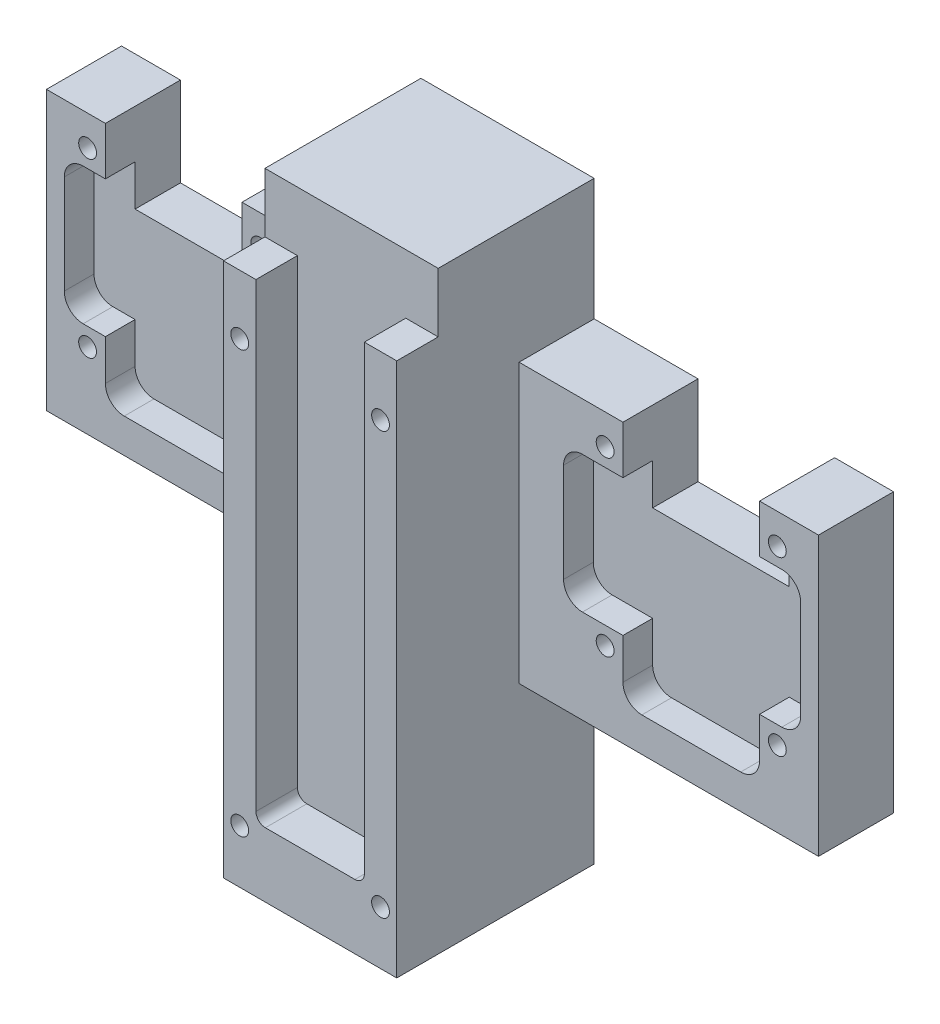
SolidWorks part; units mm, degrees
ref_plane "Front Plane" through (0, 0, 0) normal (0, 0, 1) x (1, 0, 0)
ref_plane "Top Plane" through (0, 0, 0) normal (0, 1, 0) x (1, 0, 0)
ref_plane "Right Plane" through (0, 0, 0) normal (1, 0, 0) x (0, 0, -1)
sketch "Sketch1" plane through (0, 0, 0) normal (0, 0, 1) x (1, 0, 0)
  line L0 (0, 0) -> (130, 0)
  line L1 (0, 0) -> (0, -104.86)
  line L2 (0, -104.86) -> (130, -104.86)
  line L3 (130, -104.86) -> (130, 0)
  dimension "D1" = 130
  dimension "D2" = 104.86
extrude "Boss-Extrude1" add sketch "Sketch1" along normal blind 39.84
sketch "Sketch2" plane through (0, 0, 39.84) normal (0, 0, 1) x (1, 0, 0)
  line L0 (130, 0) -> (130, -94.86)
  line L1 (130, -104.86) -> (130, 0) construction
  line L2 (130, -94.86) -> (0, -94.86)
  line L3 (0, 0) -> (0, -104.86) construction
  line L4 (0, -94.86) -> (0, 0)
  line L5 (0, 0) -> (130, 0)
  dimension "D1" = 94.86
extrude "Cut-Extrude1" cut sketch "Sketch2" against normal blind 6.6
sketch "Sketch3" plane through (0, 0, 33.24) normal (0, 0, 1) x (1, 0, 0)
  line L0 (55.875, 0) -> (55.875, -89.15)
  line L1 (130, 0) -> (0, 0) construction
  line L2 (55.875, -89.15) -> (74.125, -89.15)
  line L3 (74.125, -89.15) -> (74.125, 0)
  line L4 (74.125, 0) -> (55.875, 0)
  line L5 (130, -94.86) -> (130, 0) construction
  dimension "D1" = 18.25
  dimension "D2" = 55.875
  dimension "D3" = 89.15
extrude "Cut-Extrude2" cut sketch "Sketch3" against normal blind 6.98
sketch "Sketch5" plane through (0, 0, 33.24) normal (0, 0, 1) x (1, 0, 0)
  line L0 (79.585, 0) -> (79.585, -94.86)
  line L1 (130, 0) -> (74.125, 0) construction
  line L2 (0, -94.86) -> (130, -94.86) construction
  line L3 (79.585, -94.86) -> (130, -94.86)
  line L4 (130, -94.86) -> (130, 0)
  line L5 (130, 0) -> (79.585, 0)
  line L6 (50.415, 0) -> (50.415, -94.86)
  line L7 (55.875, 0) -> (0, 0) construction
  line L8 (50.415, -94.86) -> (0, -94.86)
  line L9 (0, -94.86) -> (0, 0)
  line L10 (0, 0) -> (50.415, 0)
  line L11 (55.875, 0) -> (55.875, -89.15) construction
  line L12 (74.125, -89.15) -> (74.125, 0) construction
  dimension "D1" = 5.46
  dimension "D2" = 5.46
extrude "Cut-Extrude3" cut sketch "Sketch5" against normal blind 20.6
sketch "Sketch6" plane through (0, 0, 12.64) normal (0, 0, 1) x (1, 0, 0)
  line L0 (50.415, -94.86) -> (50.415, 0) construction
  line L1 (74.125, 0) -> (55.875, 0) construction
  line L2 (79.585, 0) -> (79.585, -94.86) construction
  circle A0 centre (35.925, -25.6) radius 1.5
  circle A1 centre (6.925, -25.6) radius 1.5
  circle A2 centre (35.925, -54.6) radius 1.5
  circle A3 centre (6.925, -54.6) radius 1.5
  circle A4 centre (94.075, -25.6) radius 1.5
  circle A5 centre (123.075, -25.6) radius 1.5
  circle A6 centre (94.075, -54.6) radius 1.5
  circle A7 centre (123.075, -54.6) radius 1.5
  dimension "D2" = 3
  dimension "D3" = 25.6
  dimension "D4" = 29
  dimension "D5" = 29
  dimension "D6" = 29
  dimension "D8" = 14.49
  dimension "D9" = 29
  dimension "D10" = 29
  dimension "D11" = 29
  dimension "D1" = 14.49
  dimension "D7" = 29
  dimension "D12" = 29
  dimension "D13" = 25.6
extrude "Cut-Extrude4" cut sketch "Sketch6" against normal blind 12.4
sketch "Sketch7" plane through (0, 0, 12.64) normal (0, 0, 1) x (1, 0, 0)
  line L0 (50.415, -94.86) -> (50.415, 0) construction
  line L1 (0, 0) -> (50.415, 0)
  line L2 (0, 0) -> (0, -20.5)
  line L3 (0, -20.5) -> (50.415, -20.5)
  line L4 (50.415, 0) -> (50.415, -20.5)
  line L5 (130, -94.86) -> (130, 0) construction
  line L6 (79.585, 0) -> (130, 0)
  line L7 (79.585, 0) -> (79.585, -20.5)
  line L8 (79.585, -20.5) -> (130, -20.5)
  line L9 (130, 0) -> (130, -20.5)
  dimension "D1" = 20.5
  dimension "D2" = 20.5
extrude "Cut-Extrude5" cut sketch "Sketch7" against normal blind 12.4
sketch "Sketch9" plane through (0, 0, 12.64) normal (0, 0, 1) x (1, 0, 0)
  line L0 (97.075, -20.5) -> (97.075, -35.5)
  line L1 (79.585, -20.5) -> (130, -20.5) construction
  line L2 (97.075, -35.5) -> (120.075, -35.5)
  line L3 (120.075, -35.5) -> (120.075, -20.5)
  line L4 (120.075, -20.5) -> (97.075, -20.5)
  line L5 (9.925, -20.5) -> (9.925, -35.5)
  line L6 (0, -20.5) -> (50.415, -20.5) construction
  line L7 (9.925, -35.5) -> (32.925, -35.5)
  line L8 (32.925, -35.5) -> (32.925, -20.5)
  line L9 (0, -20.5) -> (50.415, -20.5) construction
  line L10 (32.925, -20.5) -> (9.925, -20.5)
  circle A0 centre (123.075, -25.6) radius 1.5 construction
  circle A1 centre (94.075, -25.6) radius 1.5 construction
  circle A2 centre (6.925, -25.6) radius 1.5 construction
  circle A3 centre (35.925, -25.6) radius 1.5 construction
  dimension "D1" = 3
  dimension "D4" = 3
  dimension "D2" = 3
  dimension "D3" = 15
  dimension "D5" = 3
  dimension "D6" = 15
extrude "Cut-Extrude7" cut sketch "Sketch9" against normal up to surface (12.4 mm away) up to face at (104.7925, -10.25, 0.24)
sketch "Sketch10" plane through (0, 0, 12.64) normal (0, 0, 1) x (1, 0, 0)
  line L0 (9.925, -28.6) -> (3, -28.6)
  line L1 (9.925, -35.5) -> (9.925, -20.5) construction
  line L2 (3, -28.6) -> (3, -51.6)
  line L3 (3, -51.6) -> (9.925, -51.6)
  line L4 (9.925, -51.6) -> (9.925, -61.6)
  line L5 (9.925, -61.6) -> (32.925, -61.6)
  line L6 (32.925, -61.6) -> (32.925, -51.6)
  line L7 (32.925, -51.6) -> (42.925, -51.6)
  line L8 (42.925, -51.6) -> (42.925, -28.6)
  line L9 (42.925, -28.6) -> (32.925, -28.6)
  line L10 (32.925, -35.5) -> (32.925, -20.5) construction
  line L11 (32.925, -28.6) -> (32.925, -35.5)
  line L12 (32.925, -35.5) -> (9.925, -35.5)
  line L13 (32.925, -35.5) -> (9.925, -35.5) construction
  line L14 (9.925, -35.5) -> (9.925, -28.6)
  line L16 (0, -20.5) -> (0, -94.86) construction
  line L17 (97.075, -28.6) -> (87.075, -28.6)
  line L18 (97.075, -20.5) -> (97.075, -35.5) construction
  line L19 (87.075, -28.6) -> (87.075, -51.6)
  line L20 (87.075, -51.6) -> (97.075, -51.6)
  line L21 (97.075, -51.6) -> (97.075, -61.6)
  line L22 (97.075, -61.6) -> (120.075, -61.6)
  line L23 (120.075, -61.6) -> (120.075, -51.6)
  line L24 (120.075, -51.6) -> (127, -51.6)
  line L25 (127, -51.6) -> (127, -28.6)
  line L26 (127, -28.6) -> (120.075, -28.6)
  line L27 (120.075, -35.5) -> (120.075, -20.5) construction
  line L28 (120.075, -28.6) -> (120.075, -35.5)
  line L29 (120.075, -35.5) -> (97.075, -35.5)
  line L30 (97.075, -35.5) -> (97.075, -28.6)
  line L31 (130, -94.86) -> (130, -20.5) construction
  circle A0 centre (6.925, -25.6) radius 1.5 construction
  circle A1 centre (35.925, -25.6) radius 1.5 construction
  circle A2 centre (6.925, -54.6) radius 1.5 construction
  circle A3 centre (6.925, -54.6) radius 1.5 construction
  circle A4 centre (35.925, -54.6) radius 1.5 construction
  circle A5 centre (94.075, -25.6) radius 1.5 construction
  circle A6 centre (94.075, -54.6) radius 1.5 construction
  circle A7 centre (123.075, -54.6) radius 1.5 construction
  circle A8 centre (123.075, -25.6) radius 1.5 construction
  dimension "D3" = 3
  dimension "D6" = 3
  dimension "D10" = 3
  dimension "D14" = 3
  dimension "D1" = 3
  dimension "D2" = 3
  dimension "D4" = 3
  dimension "D5" = 3
  dimension "D7" = 10
  dimension "D8" = 3
  dimension "D9" = 10
  dimension "D11" = 3
  dimension "D12" = 3
  dimension "D13" = 3
  dimension "D15" = 3
  dimension "D16" = 10
  dimension "D17" = 3
  dimension "D18" = 10
extrude "Cut-Extrude8" cut sketch "Sketch10" against normal blind 5
sketch "Sketch11" plane through (0, 0, 33.24) normal (0, 0, 1) x (1, 0, 0)
  line L0 (55.875, 0) -> (50.415, 0) construction
  line L1 (55.875, 0) -> (55.875, -89.15) construction
  line L2 (74.125, -89.15) -> (74.125, 0) construction
  line L3 (79.585, 0) -> (74.125, 0) construction
  circle A0 centre (53.145, -20) radius 1.5
  circle A1 centre (76.855, -20) radius 1.5
  circle A2 centre (53.145, -91) radius 1.5
  circle A3 centre (76.855, -91) radius 1.5
  point P4 (53.145, 0)
  dimension "D1" = 20
  dimension "D2" = 2.73
  dimension "D3" = 2.73
  dimension "D5" = 91
  dimension "D4" = 20
extrude "Cut-Extrude9" cut sketch "Sketch11" against normal blind 15
fillet "Fillet2" radius 3.175 1 edges at (3, -51.6, 10.14)
fillet "Fillet3" radius 3.175 15 edges at (120.075, -61.6, 10.14) (97.075, -61.6, 10.14) (127, -28.6, 10.14) (127, -51.6, 10.14) (87.075, -28.6, 10.14) (87.075, -51.6, 10.14) (79.585, -20.5, 6.44) (50.415, -20.5, 6.44) (32.925, -35.5, 3.94) (9.925, -35.5, 3.94) (3, -28.6, 10.14) (42.925, -28.6, 10.14) (42.925, -51.6, 10.14) (32.925, -61.6, 10.14) (9.925, -61.6, 10.14)
fillet "Fillet4" radius 3.175 2 edges at (120.075, -35.5, 3.94) (97.075, -35.5, 3.94)
fillet "Fillet5" radius 1.5875 2 edges at (74.125, -89.15, 29.75) (55.875, -89.15, 29.75)
fillet "Fillet6" radius 3.175 2 edges at (79.585, -94.86, 22.94) (50.415, -94.86, 22.94)
sketch "Sketch12" plane through (0, 0, 39.84) normal (0, 0, 1) x (1, 0, 0)
  line L0 (0, -67.36) -> (50.415, -67.36)
  line L1 (0, -20.5) -> (0, -94.86) construction
  line L2 (50.415, -91.685) -> (50.415, -17.325) construction
  line L3 (50.415, -67.36) -> (50.415, -95.14)
  line L4 (50.415, -95.14) -> (50.415, -104.86)
  line L5 (0, -104.86) -> (130, -104.86) construction
  line L6 (50.415, -104.86) -> (0, -104.86)
  line L7 (0, -104.86) -> (0, -67.36)
  line L8 (79.585, -67.36) -> (79.585, -104.86)
  line L9 (79.585, 0) -> (79.585, -91.685) construction
  line L10 (79.585, -104.86) -> (130, -104.86)
  line L11 (130, -104.86) -> (130, -67.36)
  line L12 (130, -94.86) -> (130, -20.5) construction
  line L13 (130, -67.36) -> (79.585, -67.36)
  line L14 (50.415, -100) -> (79.585, -100)
  line L15 (79.585, -100) -> (79.585, -104.86)
  line L16 (74.125, 0) -> (55.875, 0) construction
  line L17 (0, -20.5) -> (50.415, -20.5)
  line L18 (50.415, -20.5) -> (50.415, 0)
  line L19 (50.415, 0) -> (0, 0)
  line L20 (0, 0) -> (0, -20.5)
  line L21 (79.585, 0) -> (130, 0)
  line L22 (130, 0) -> (130, -20.5)
  line L23 (130, -20.5) -> (79.585, -20.5)
  line L24 (79.585, -17.325) -> (79.585, -91.685) construction
  line L25 (79.585, -20.5) -> (79.585, 0)
  line L26 (97.075, -20.5) -> (97.075, -35.5)
  line L27 (120.075, -20.5) -> (120.075, -35.5)
  line L28 (120.075, -35.5) -> (97.075, -35.5)
  line L29 (32.925, -20.5) -> (32.925, -35.5)
  line L30 (9.925, -20.5) -> (9.925, -35.5)
  line L31 (9.925, -35.5) -> (32.925, -35.5)
  line M6 (130, -94.86) -> (0, -94.86)
  line M7 (0, -94.86) -> (0, -104.86)
  line M8 (0, -104.86) -> (130, -104.86)
  line M9 (130, -104.86) -> (130, -94.86)
  dimension "D1" = 37.5
  dimension "D2" = 37.5
  dimension "D3" = 100
extrude "Cut-Extrude11" cut sketch "Sketch12" against normal blind 42 contours L19 L20 L17 L18 | L25 L23 L22 L21 | L28 L27 L23 L26 | L30 L31 L29 L17 | L7 L3 L0 M6 | L11 L13 L8 M6 | L8 M6 M8 M9 | L4 L3 M6 M7 M8 | L14 L4 L8 M8
sketch "Sketch13" plane through (79.585, 0, 0) normal (1, 0, 0) x (0, 0, -1)
  line L0 (-33.24, -94.86) -> (-33.24, -100)
  line L1 (0, -100) -> (-39.84, -100) construction
  line L2 (-33.24, -100) -> (-39.84, -100)
  line L3 (-39.84, -100) -> (-39.84, -94.86)
  line L4 (-39.84, -94.86) -> (-33.24, -94.86)
extrude "Cut-Extrude12" cut sketch "Sketch13" against normal through all
sketch "Sketch14" plane through (0, 0, 33.24) normal (0, 0, 1) x (1, 0, 0)
  line L0 (50.415, 0) -> (50.415, -10)
  line L1 (50.415, -100) -> (50.415, 0) construction
  line L2 (50.415, -10) -> (79.585, -10)
  line L4 (79.585, 0) -> (79.585, -100) construction
  line L5 (79.585, -10) -> (79.585, 0)
  line L6 (79.585, 0) -> (50.415, 0)
  dimension "D1" = 10
extrude "Cut-Extrude14" cut sketch "Sketch14" along direction (0, 0, 1) on the side against the normal up to surface (6.98 mm away)
sketch "Sketch15" plane through (0, 0, 0) normal (0, 0, -1) x (-1, 0, 0)
  line L0 (-73.585, -100) -> (-56.415, -100)
  line L1 (-50.415, -100) -> (-79.585, -100) construction
  line L2 (-56.415, -100) -> (-56.415, -23.5)
  line L3 (-59.915, -20) -> (-70.085, -20)
  line L4 (-73.585, -23.5) -> (-73.585, -100)
  line L5 (-79.585, -67.36) -> (-79.585, -100) construction
  line L6 (-50.415, -67.36) -> (-50.415, -100) construction
  arc A0 (-70.085, -20) -> (-73.585, -23.5) centre (-70.085, -23.5) ccw
  arc A1 (-59.915, -20) -> (-56.415, -23.5) centre (-59.915, -23.5) cw
  dimension "D4" = 3.5
  dimension "D1" = 6
  dimension "D2" = 6
  dimension "D3" = 80
extrude "Cut-Extrude15" cut sketch "Sketch15" against normal blind 9
